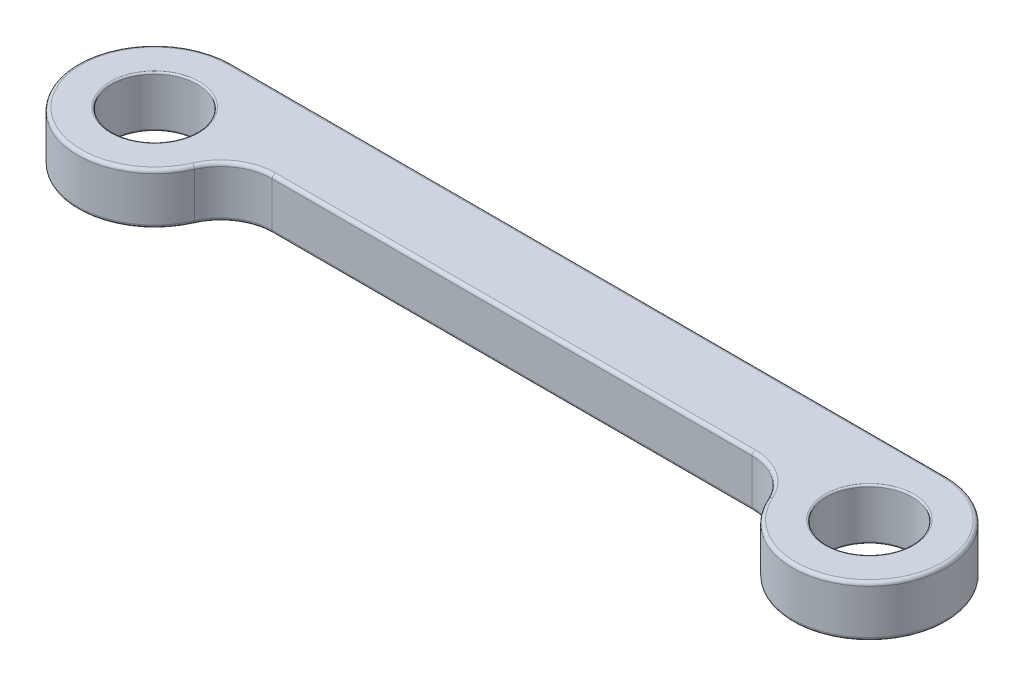
SolidWorks part; units mm, degrees
ref_plane "前视基准面" through (0, 0, 0) normal (0, 0, 1) x (1, 0, 0)
ref_plane "上视基准面" through (0, 0, 0) normal (0, 1, 0) x (1, 0, 0)
ref_plane "右视基准面" through (0, 0, 0) normal (1, 0, 0) x (0, 0, -1)
sketch "草图1" plane through (0, 0, 0) normal (0, 1, 0) x (1, 0, 0)
  line L0 (-41.83, 0) -> (41.83, 0) construction
  line L1 (-41.83, 9) -> (41.83, 9)
  line L2 (-28.0823, 0) -> (28.0823, 0)
  circle A0 centre (-41.83, 0) radius 5
  circle A1 centre (41.83, 0) radius 5
  arc A2 (-41.83, 9) -> (-33.5814, -3.6) centre (-41.83, 0) ccw
  arc A3 (33.5814, -3.6) -> (41.83, 9) centre (41.83, 0) ccw
  arc A4 (33.5814, -3.6) -> (28.0823, 0) centre (28.0823, -6) ccw
  circle A5 centre (-41.83, 0) radius 9 construction
  circle A6 centre (41.83, 0) radius 9 construction
  arc A7 (-33.5814, -3.6) -> (-28.0823, 0) centre (-28.0823, -6) cw
  point P4 (0, 0)
  point P8 (50.83, 0)
  point P15 (-32.83, 0)
  point P19 (32.83, 0)
  point P22 (-32.83, 0)
  dimension "D2" = 10
  dimension "D4" = 6
  dimension "D1" = 83.66
  dimension "D3" = 4
extrude "凸台-拉伸1" add sketch "草图1" along normal blind 6
fillet "圆角1" radius 0.2 4 edges at (-41.83, 6, 5) (41.83, 6, 5) (-41.83, 0, 5) (41.83, 0, 5)
fillet "圆角2" radius 0.4 12 edges at (49.3599, 0, 4.9295) (0, 0, -9) (-49.3599, 0, 4.9295) (-31.3686, 0, 0.98) (0, 0, 0) (31.3686, 0, 0.98) (0, 6, 0) (-31.3686, 6, 0.98) (-49.3599, 6, 4.9295) (0, 6, -9) (49.3599, 6, 4.9295) (31.3686, 6, 0.98)
